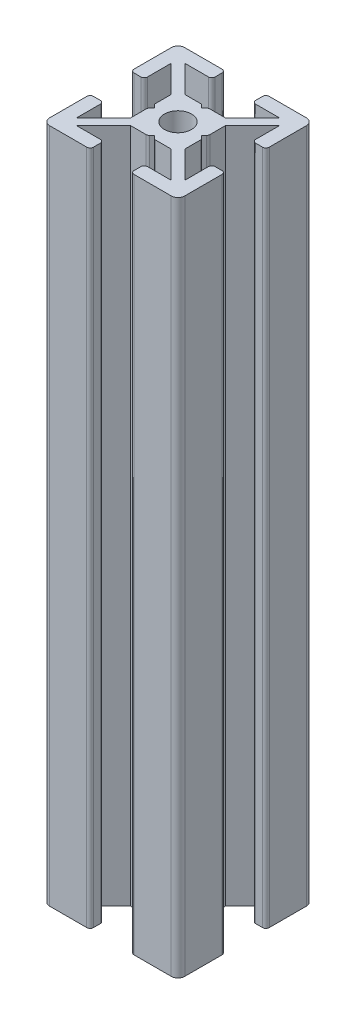
SolidWorks part; units mm, degrees
ref_plane "Front Plane" through (0, 0, 0) normal (0, 0, 1) x (1, 0, 0)
ref_plane "Top Plane" through (0, 0, 0) normal (0, 1, 0) x (1, 0, 0)
ref_plane "Right Plane" through (0, 0, 0) normal (1, 0, 0) x (0, 0, -1)
sketch "Sketch1" plane through (0, 0, 0) normal (0, 1, 0) x (1, 0, 0)
  line L0 (7, 20) -> (7, 18)
  line L1 (0, 0) -> (20, 0)
  line L2 (0, 0) -> (0, 20)
  line L3 (0, 20) -> (20, 20)
  line L4 (20, 0) -> (20, 20)
  line L5 (7, 18) -> (3, 18)
  line L6 (3, 18) -> (7, 14)
  line L7 (7, 14) -> (13, 14)
  line L8 (13, 14) -> (17, 18)
  line L9 (17, 18) -> (13, 18)
  line L10 (13, 18) -> (13, 20)
  line L11 (13, 20) -> (7, 20)
  line L12 (20, 7) -> (20, 13)
  line L13 (20, 13) -> (18, 13)
  line L14 (18, 13) -> (18, 17)
  line L15 (18, 17) -> (14, 13)
  line L16 (14, 13) -> (14, 7)
  line L17 (14, 7) -> (18, 3)
  line L18 (18, 3) -> (18, 7)
  line L19 (18, 7) -> (20, 7)
  line L20 (7, 0) -> (13, 0)
  line L21 (13, 0) -> (13, 2)
  line L22 (13, 2) -> (17, 2)
  line L23 (17, 2) -> (13, 6)
  line L24 (13, 6) -> (7, 6)
  line L25 (7, 6) -> (3, 2)
  line L26 (3, 2) -> (7, 2)
  line L27 (7, 2) -> (7, 0)
  line L28 (0, 13) -> (0, 7)
  line L29 (0, 7) -> (2, 7)
  line L30 (2, 7) -> (2, 3)
  line L31 (2, 3) -> (6, 7)
  line L32 (6, 7) -> (6, 13)
  line L33 (6, 13) -> (2, 17)
  line L34 (2, 17) -> (2, 13)
  line L35 (2, 13) -> (0, 13)
  line L36 (9.5, 14) -> (10.5, 14)
  line L37 (10.5, 14) -> (10, 13.5)
  line L38 (10, 13.5) -> (9.5, 14)
  line L39 (13.5, 10) -> (14, 10.5)
  line L40 (14, 10.5) -> (14, 9.5)
  line L41 (14, 9.5) -> (13.5, 10)
  line L42 (10, 6.5) -> (10.5, 6)
  line L43 (10.5, 6) -> (9.5, 6)
  line L44 (9.5, 6) -> (10, 6.5)
  line L45 (6.5, 10) -> (6, 9.5)
  line L46 (6, 9.5) -> (6, 10.5)
  line L47 (6, 10.5) -> (6.5, 10)
  circle A0 centre (10, 10) radius 2
  point P10 (10, 10)
  point P41 (10, 10)
  point P43 (10, 14)
  point P57 (10, 10)
  dimension "D8" = 4
  dimension "D1" = 20
  dimension "D2" = 20
  dimension "D3" = 7
  dimension "D4" = 7
  dimension "D5" = 6
  dimension "D6" = 4
  dimension "D7" = 4
  dimension "D9" = 0.5
  dimension "D11" = 0.5
  dimension "D12" = 0.5
  dimension "D13" = 4
  dimension "D10" = 4
extrude "Boss-Extrude1" add sketch "Sketch1" along normal blind 100 contours L35 L34 L33 L32 L31 L30 L29 L2 L1 L27 L26 L25 L24 L23 L22 L21 L4 L19 L18 L17 L16 L15 L14 L13 L3 L10 L9 L8 L7 L6 L5 L0 A0
fillet "Fillet1" radius 1 4 edges at (0, 50, -20) (0, 50, 0) (20, 50, 0) (20, 50, -20)
fillet "Fillet2" radius 0.5 16 edges at (20, 50, -13) (18, 50, -13) (20, 50, -7) (18, 50, -7) (13, 50, -2) (13, 50, 0) (7, 50, 0) (7, 50, -2) (0, 50, -7) (2, 50, -7) (13, 50, -20) (13, 50, -18) (7, 50, -20) (7, 50, -18) (0, 50, -13) (2, 50, -13)
fillet "Fillet4" radius 0.5 8 edges at (10.5, 50, -6) (9.5, 50, -6) (6, 50, -9.5) (6, 50, -10.5) (10.5, 50, -14) (9.5, 50, -14) (14, 50, -9.5) (14, 50, -10.5)
